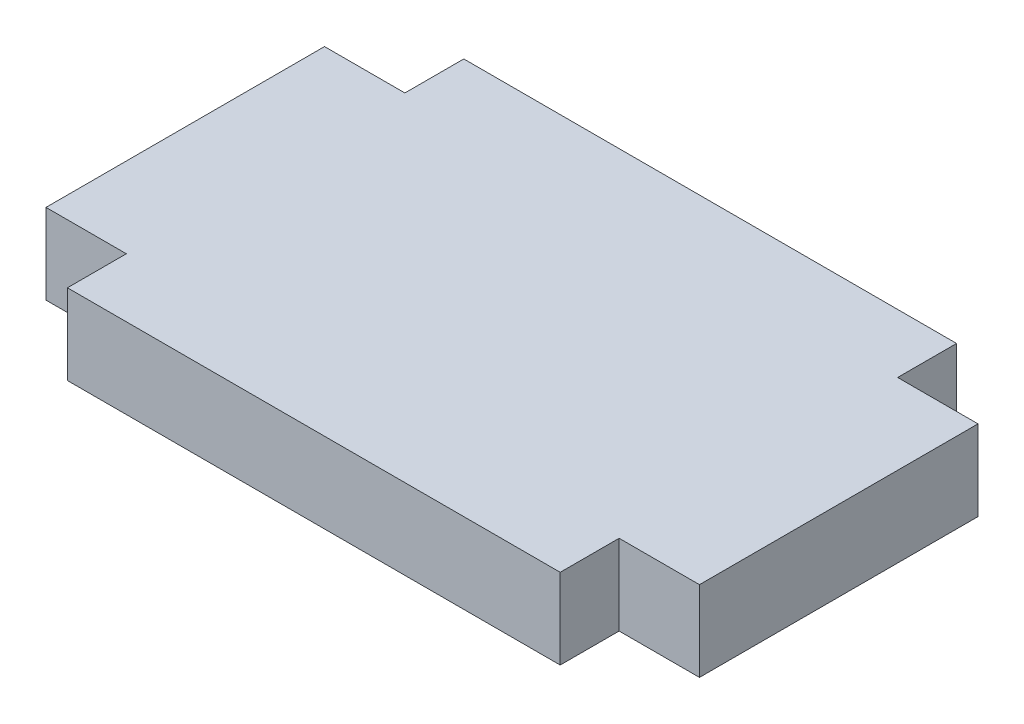
SolidWorks part; units mm, degrees
ref_plane "Front Plane" through (0, 0, 0) normal (0, 0, 1) x (1, 0, 0)
ref_plane "Top Plane" through (0, 0, 0) normal (0, 1, 0) x (1, 0, 0)
ref_plane "Right Plane" through (0, 0, 0) normal (1, 0, 0) x (0, 0, -1)
sketch "Sketch1" plane through (0, 0, 0) normal (0, 1, 0) x (1, 0, 0)
  line L0 (67.945, -46.99) -> (67.945, -40.005)
  line L1 (0, 0) -> (77.47, 0)
  line L2 (0, 0) -> (0, -46.99)
  line L3 (0, -46.99) -> (77.47, -46.99)
  line L4 (77.47, 0) -> (77.47, -46.99)
  line L5 (67.945, -40.005) -> (77.47, -40.005)
  line L6 (77.47, -6.985) -> (67.945, -6.985)
  line L7 (67.945, -6.985) -> (67.945, 0)
  line L8 (0, -6.985) -> (9.525, -6.985)
  line L9 (9.525, -6.985) -> (9.525, 0)
  line L10 (0, -40.005) -> (9.525, -40.005)
  line L11 (9.525, -40.005) -> (9.525, -46.99)
  point P16 (72.7075, -6.985)
  dimension "D1" = 77.47
  dimension "D2" = 46.99
  dimension "D3" = 33.02
  dimension "D4" = 9.525
  dimension "D5" = 9.525
  dimension "D6" = 33.02
  dimension "D7" = 9.525
  dimension "D9" = 9.525
extrude "Boss-Extrude1" add sketch "Sketch1" along normal blind 9.525 contours L10 L11 L3 L0 L5 L4 L6 L7 L1 L9 L8 L2
